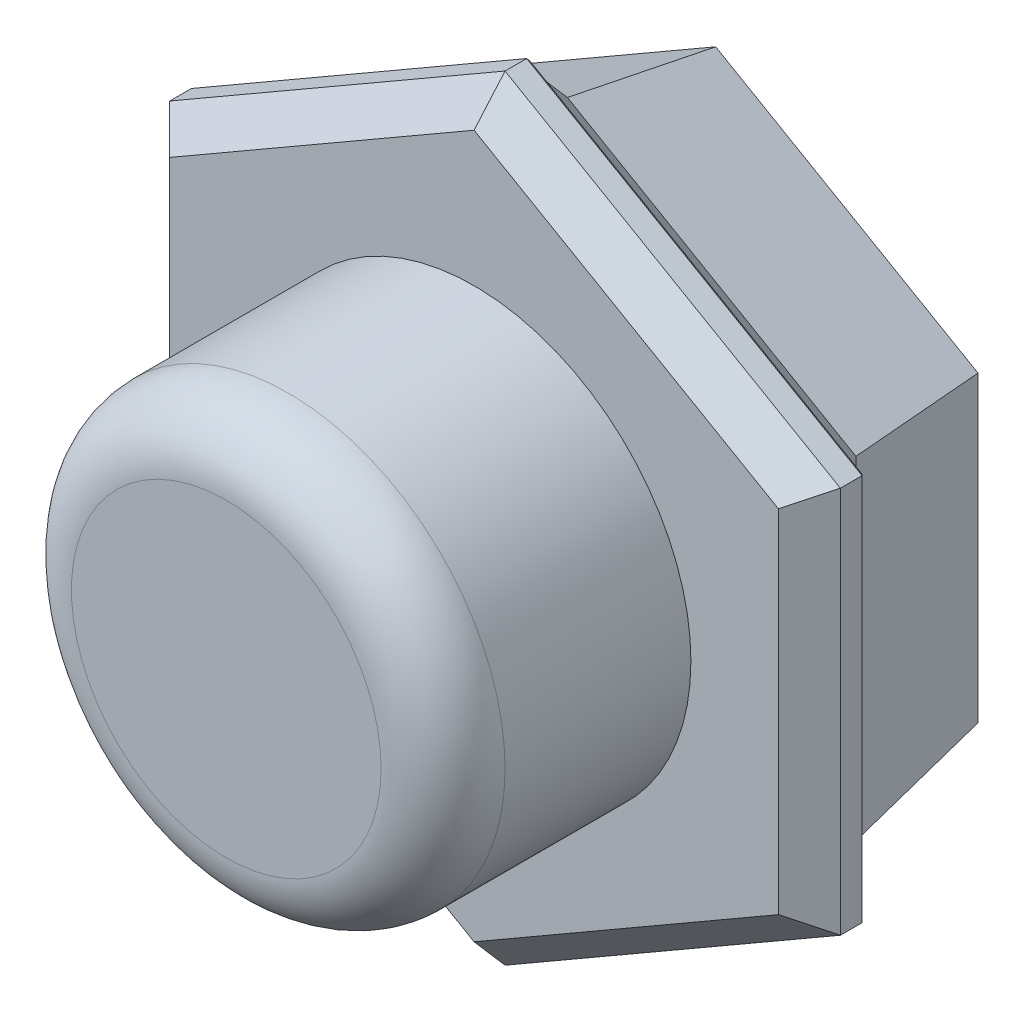
SolidWorks part; units mm, degrees
material "ABS"
ref_plane "Front Plane" through (0, 0, 0) normal (0, 0, 1) x (1, 0, 0)
ref_plane "Top Plane" through (0, 0, 0) normal (0, 1, 0) x (1, 0, 0)
ref_plane "Right Plane" through (0, 0, 0) normal (1, 0, 0) x (0, 0, -1)
sketch "Sketch1" plane through (0, 0, 0) normal (0, 0, 1) x (1, 0, 0)
  line L0 (0, -6.25) -> (0, 6.25) construction
  line L1 (0, 6.25) -> (-5.4127, 3.125)
  line L2 (-5.4127, 3.125) -> (-5.4127, -3.125)
  line L3 (-5.4127, -3.125) -> (0, -6.25)
  line L4 (0, -6.25) -> (5.4127, -3.125)
  line L5 (5.4127, -3.125) -> (5.4127, 3.125)
  line L6 (5.4127, 3.125) -> (0, 6.25)
  circle A0 centre (0, 0) radius 5.4127 construction
  dimension "D1" = 12.5
extrude "Boss-Extrude1" add sketch "Sketch1" along normal blind 0.9
chamfer "Chamfer1" distance 0.5 angle 45 6 edges at (5.4127, 0, 0.9) (2.7063, -4.6875, 0.9) (-2.7063, -4.6875, 0.9) (-5.4127, 0, 0.9) (-2.7063, 4.6875, 0.9) (2.7063, 4.6875, 0.9)
sketch "Sketch5" plane through (0, 0, 0.9) normal (0, 0, 1) x (1, 0, 0)
  circle A0 centre (0, 0) radius 3.5
  dimension "D1" = 7
extrude "Boss-Extrude5" add sketch "Sketch5" along normal blind 4
fillet "Fillet2" radius 1 1 edges at (3.5, 0, 4.9)
sketch "Sketch6" plane through (0, 0, 0) normal (0, 0, -1) x (-1, 0, 0)
  line L0 (0, -5.5) -> (0, 5.5) construction
  line L1 (0, 5.5) -> (-4.7631, 2.75)
  line L2 (-4.7631, 2.75) -> (-4.7631, -2.75)
  line L3 (-4.7631, -2.75) -> (0, -5.5)
  line L4 (0, -5.5) -> (4.7631, -2.75)
  line L5 (4.7631, -2.75) -> (4.7631, 2.75)
  line L6 (4.7631, 2.75) -> (0, 5.5)
  circle A0 centre (0, 0) radius 4.7631 construction
  dimension "D1" = 11
extrude "Boss-Extrude6" add sketch "Sketch6" along normal blind 3 draft 10
chamfer "Chamfer2" distance 0.5 angle 45 6 edges at (-2.3816, 4.125, 0) (-4.7631, 0, 0) (-2.3816, -4.125, 0) (2.3816, -4.125, 0) (4.7631, 0, 0) (2.3816, 4.125, 0)
sketch "Sketch7" plane through (0, 0, -3) normal (0, 0, -1) x (-1, 0, 0)
  line L0 (-4.8281, -3.6637) -> (4.4434, -3.6637) construction
  text T0 "4" font "Verdana" height 7
extrude "Cut-Extrude1" cut sketch "Sketch7" against normal blind 0.5
sketch "Sketch8" plane through (0, 0, -3) normal (0, 0, -1) x (-1, 0, 0)
  line L3 (0.4722, 2.2051) -> (-2.2082, -0.9169)
  line L4 (-2.2082, -0.9169) -> (0.4722, -0.9169)
  line L5 (0.4722, -0.9169) -> (0.4722, 2.2051)
  line L6 (0.4722, 2.2051) -> (-2.2082, -0.9169)
  line L7 (-2.2082, -0.9169) -> (0.4722, -0.9169)
  line L8 (0.4722, -0.9169) -> (0.4722, 2.2051)
  dimension "D1" = 0
extrude "Cut-Extrude2" cut sketch "Sketch8" against normal up to surface (0.5 mm away) up to face at (0.4213, 0.1238, -2.5)
chamfer "Chamfer3" distance 0.05 angle 45 6 edges at (5.4127, 0, 0) (2.7063, -4.6875, 0) (-2.7063, -4.6875, 0) (-5.4127, 0, 0) (-2.7063, 4.6875, 0) (2.7063, 4.6875, 0)
